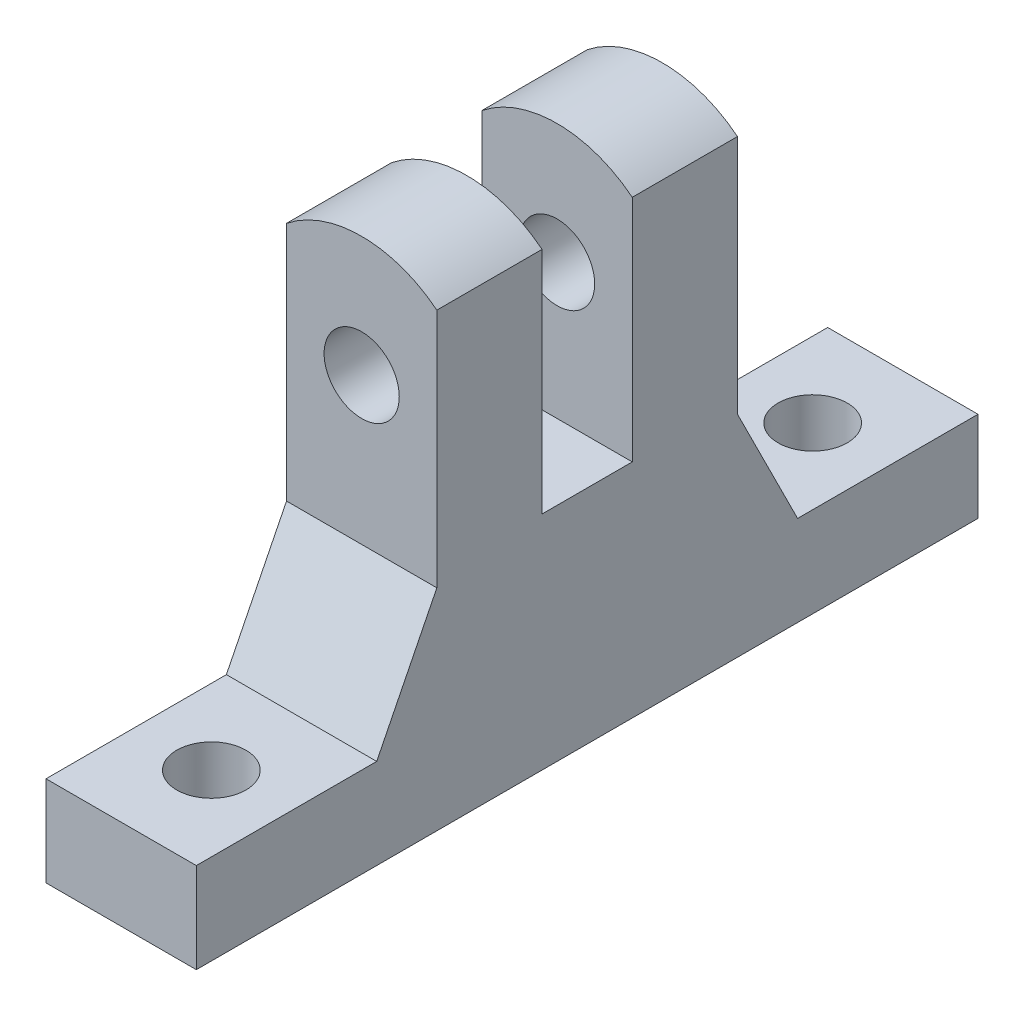
SolidWorks part; units mm, degrees
ref_plane "Front Plane" through (0, 0, 0) normal (0, 0, 1) x (1, 0, 0)
ref_plane "Top Plane" through (0, 0, 0) normal (0, 1, 0) x (1, 0, 0)
ref_plane "Right Plane" through (0, 0, 0) normal (1, 0, 0) x (0, 0, -1)
sketch "Sketch1" plane through (0, 0, 0) normal (0, 0, 1) x (1, 0, 0)
  line L0 (2.5, 15) -> (2.5, 0)
  line L1 (-2.5, 15) -> (-2.5, 0)
  line L5 (-2.5, 0) -> (2.5, 0)
  arc A1 (2.5, 15) -> (-2.5, 15) centre (0, 11.8775) ccw
  circle A3 centre (0, 11.8775) radius 1.25
  dimension "D1" = 2.5
  dimension "D2" = 4
  dimension "D3" = 15
  dimension "D4" = 5
extrude "Boss-Extrude1" add sketch "Sketch1" against normal blind 10
sketch "Sketch2" plane through (-2.5, 0, 0) normal (-1, 0, 0) x (0, 0, 1)
  line L0 (0, 15.8775) -> (-10, 15.8775) construction
  line L1 (-6.5, 15.8775) -> (-3.5, 15.8775)
  line L2 (-6.5, 15.8775) -> (-6.5, 7.3775)
  line L3 (-6.5, 7.3775) -> (-3.5, 7.3775)
  line L4 (-3.5, 15.8775) -> (-3.5, 7.3775)
  line L5 (-5, 0) -> (-5, 7.3775) construction
  line L6 (-10, 0) -> (0, 0) construction
  dimension "D1" = 8.5
  dimension "D2" = 3
extrude "Cut-Extrude1" cut sketch "Sketch2" against normal through all
sketch "Sketch3" plane through (0, 0, 0) normal (0, -1, 0) x (1, 0, 0)
  line L0 (-2.5, 0) -> (2.5, -10) construction
  line L1 (2.5, -10) -> (2.5, 0) construction
  line L2 (-2.5, -18) -> (2.5, -18)
  line L3 (-2.5, -18) -> (-2.5, 8)
  line L4 (-2.5, 8) -> (2.5, 8)
  line L5 (2.5, -18) -> (2.5, 8)
  line L6 (-2.5, -18) -> (2.5, 8) construction
  line L7 (-2.5, 8) -> (2.5, -18) construction
  line L8 (-2.5, -5) -> (2.5, -5) construction
  line L9 (0, -5) -> (0, 5) construction
  circle A0 centre (0, 5) radius 1.15
  circle A1 centre (0, -15) radius 1.15
  point P4 (0, -5)
  dimension "D1" = 2.3
  dimension "D2" = 20
  dimension "D3" = 3
extrude "Boss-Extrude2" add sketch "Sketch3" against normal blind 3
chamfer "Chamfer1" distance 2 distance2 4 1 edges at (0, 3, -10)
chamfer "Chamfer2" distance 4 distance2 2 1 edges at (0, 3, 0)
